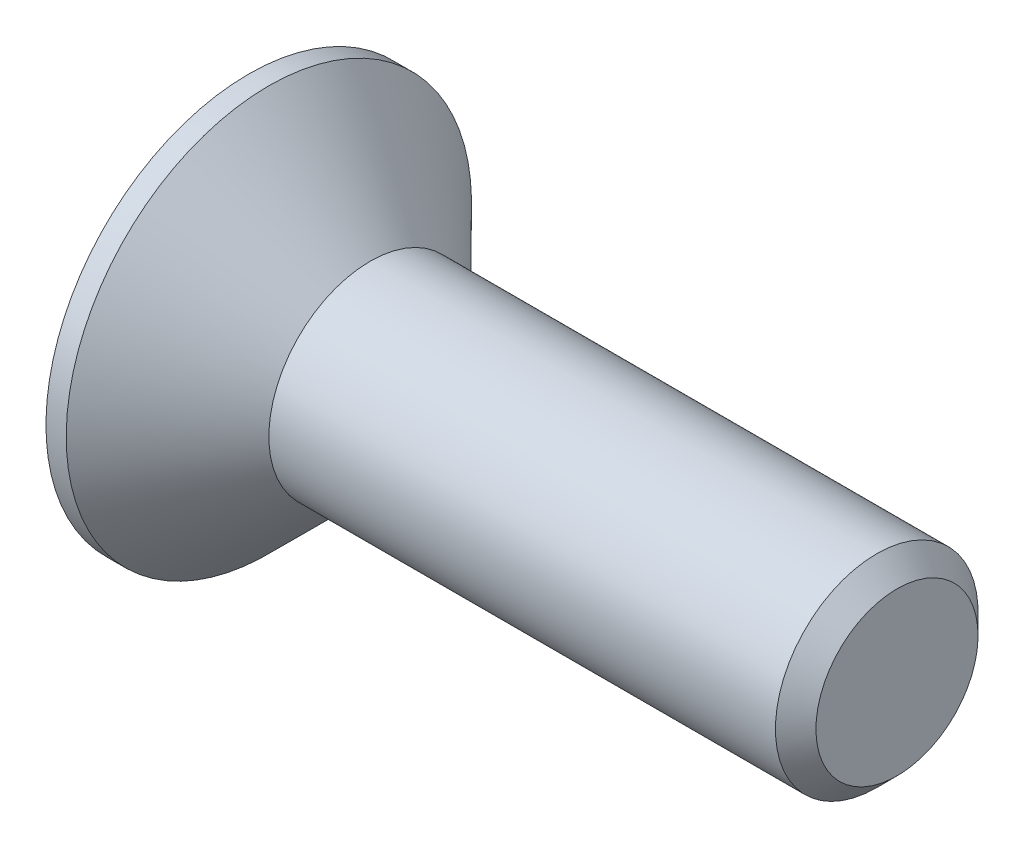
SolidWorks part; units mm, degrees
ref_plane "Plan de face" through (0, 0, 0) normal (0, 0, 1) x (1, 0, 0)
ref_plane "Plan de dessus" through (0, 0, 0) normal (0, 1, 0) x (1, 0, 0)
ref_plane "Plan de droite" through (0, 0, 0) normal (1, 0, 0) x (0, 0, -1)
sketch "Esquisse1" plane through (0, 0, 0) normal (0, 0, 1) x (1, 0, 0)
  line L0 (0, 0) -> (0, 5)
  line L1 (0, 5) -> (0.5, 5)
  line L2 (0.5, 5) -> (3, 2.5)
  line L3 (3, 2.5) -> (16, 2.5)
  line L4 (16, 2.5) -> (16, 0)
  line L5 (16, 0) -> (0, 0) construction
  line L6 (0, 0) -> (16, 0)
  dimension "D1" = 3
  dimension "D2" = 16
  dimension "D3" = 5
  dimension "D4" = 10
  dimension "D5" = 45
revolve "Révolution1" add sketch "Esquisse1" angle 360 about L5
chamfer "Chanfrein1" distance 0.5 angle 45 1 edges at (16, 2.5, 0)
sketch "Esquisse2" plane through (0, 0, 0) normal (-1, 0, 0) x (0, 0, 1)
  line L1 (0, 1.7321) -> (-1.5, 0.866)
  line L2 (-1.5, 0.866) -> (-1.5, -0.866)
  line L3 (-1.5, -0.866) -> (0, -1.7321)
  line L4 (0, -1.7321) -> (1.5, -0.866)
  line L5 (1.5, -0.866) -> (1.5, 0.866)
  line L6 (1.5, 0.866) -> (0, 1.7321)
  circle A0 centre (0, 0) radius 1.5 construction
  dimension "D1" = 3
extrude "Enlèv. mat.-Extru.1" cut sketch "Esquisse2" against normal blind 2.3
